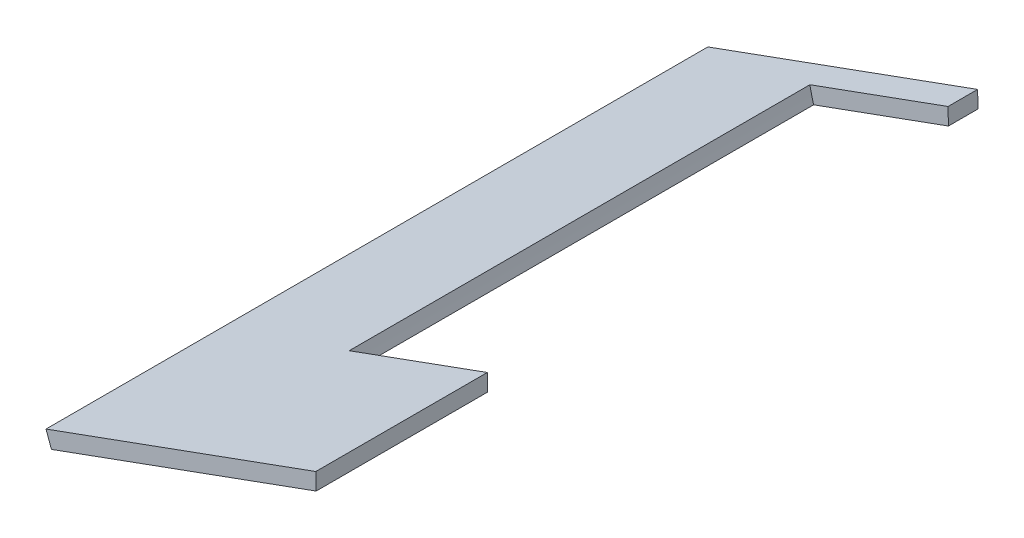
SolidWorks part; units mm, degrees
ref_plane "Front Plane" through (0, 0, 0) normal (0, 0, 1) x (1, 0, 0)
ref_plane "Top Plane" through (0, 0, 0) normal (0, 1, 0) x (1, 0, 0)
ref_plane "Right Plane" through (0, 0, 0) normal (1, 0, 0) x (0, 0, -1)
sketch "Sketch2" plane through (0, 0, 2) normal (0, 0, 1) x (1, 0, 0)
  line L1 (9867.1836, 629.0966) -> (10232.6212, 514.4475) construction
  line L3 (9824.8782, 584.8528) -> (9909.7871, 615.7306)
  line L6 (9865.6869, 624.3259) -> (10231.1244, 509.6768) construction
  line L7 (9824.8782, 584.8528) -> (9826.587, 580.1539)
  line L8 (9909.7871, 615.7306) -> (9909.9053, 610.4532)
  line L9 (9826.587, 580.1539) -> (9909.9053, 610.4532)
  line L11 (9829.5771, 586.5616) -> (9947.0505, 629.2817) construction
  line L14 (9941.3843, 264.4794) -> (9824.8782, 584.8528) construction
  circle A0 centre (9911.3826, 544.486) radius 62.5 construction
  circle A1 centre (9911.3826, 544.486) radius 67.5 construction
extrude "Boss-Extrude1" add sketch "Sketch2" along normal up to surface (208.2958 mm away)
ref_plane "Plane1" through (0, 0, 156.31) normal (0, 0, 1) x (1, 0, 0)
sketch "Sketch3" plane through (0, 0, 156.31) normal (0, 0, 1) x (1, 0, 0)
  circle A0 centre (9942.2064, 615.5926) radius 77.5
  circle A2 centre (9942.2064, 615.5926) radius 77.5 construction
extrude "Cut-Extrude1" cut sketch "Sketch3" against normal blind 145
